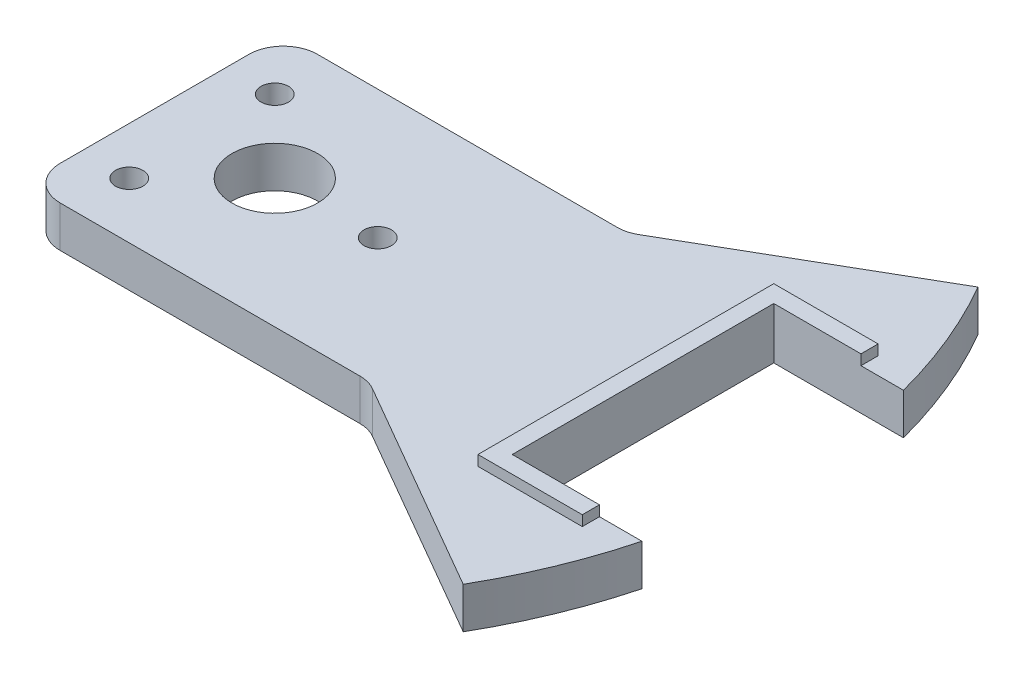
SolidWorks part; units mm, degrees
ref_plane "Front Plane" through (0, 0, 0) normal (0, 0, 1) x (1, 0, 0)
ref_plane "Top Plane" through (0, 0, 0) normal (0, 1, 0) x (1, 0, 0)
ref_plane "Right Plane" through (0, 0, 0) normal (1, 0, 0) x (0, 0, -1)
sketch "Sketch1" plane through (0, 0, 0) normal (0, 1, 0) x (1, 0, 0)
  line L0 (67.2724, 38.8397) -> (129.9038, 75)
  line L1 (0, 0) -> (150, 0) construction
  line L2 (67.2724, -38.8397) -> (129.9038, -75)
  line L4 (62.2724, 37.5) -> (-25.0481, 37.5)
  line L5 (62.2724, -37.5) -> (-25.0481, -37.5)
  line L6 (-35.0481, 27.5) -> (-35.0481, -27.5)
  line L7 (0, 0) -> (-47.1244, 0) construction
  line L8 (-21.2132, 21.2132) -> (0, 0) construction
  arc A0 (129.9038, -75) -> (129.9038, 75) centre (0, 0) ccw
  circle A1 centre (0, 0) radius 12.5
  circle A2 centre (30, 0) radius 4
  arc A5 (67.2724, 38.8397) -> (62.2724, 37.5) centre (62.2724, 47.5) cw
  arc A6 (67.2724, -38.8397) -> (62.2724, -37.5) centre (62.2724, -47.5) ccw
  arc A7 (-35.0481, -27.5) -> (-25.0481, -37.5) centre (-25.0481, -27.5) ccw
  arc A8 (-25.0481, 37.5) -> (-35.0481, 27.5) centre (-25.0481, 27.5) ccw
  circle A9 centre (-21.2132, 21.2132) radius 4
  circle A10 centre (-21.2132, -21.2132) radius 4
  point P19 (64.9519, 37.5)
  point P22 (64.9519, -37.5)
  point P25 (-35.0481, -37.5)
  point P28 (-35.0481, 37.5)
  dimension "D1" = 300
  dimension "D6" = 25
  dimension "D7" = 8
  dimension "D9" = 8
  dimension "D11" = 45
  dimension "D13" = 10
  dimension "D2" = 30
  dimension "D3" = 100
  dimension "D4" = 75
  dimension "D5" = 75
  dimension "D8" = 30
  dimension "D10" = 30
extrude "Boss-Extrude1" add sketch "Sketch1" along normal blind 12
sketch "Sketch3" plane through (0, 12, 0) normal (0, 1, 0) x (1, 0, 0)
  line L0 (0, 0) -> (150, 0) construction
  line L1 (107.3, 38.1) -> (107.3, -38.1)
  line L2 (107.3, 38.1) -> (132.7, 38.1) construction
  line L3 (107.3, 38.1) -> (107.3, -38.1) construction
  line L4 (107.3, -38.1) -> (132.7, -38.1) construction
  line L5 (132.7, 38.1) -> (132.7, -38.1) construction
  line L6 (107.3, 38.1) -> (132.7, -38.1) construction
  line L7 (107.3, -38.1) -> (132.7, 38.1) construction
  line L8 (107.3, 38.1) -> (155.3028, 38.1)
  line L9 (107.3, -38.1) -> (155.3028, -38.1)
  line L10 (155.3028, 38.1) -> (155.3028, -38.1)
  arc A0 (129.9038, -75) -> (129.9038, 75) centre (0, 0) ccw construction
  point P6 (120, 0)
  dimension "D1" = 25.4
  dimension "D2" = 76.2
  dimension "D3" = 120
extrude "Cut-Extrude5" cut sketch "Sketch3" against normal through all
sketch "Sketch4" plane through (0, 12, 0) normal (0, 1, 0) x (1, 0, 0)
  line L0 (0, 0) -> (145.9243, 0) construction
  line L1 (107.3, 38.1) -> (132.7, 38.1)
  line L3 (132.7, 38.1) -> (132.7, 43.1)
  line L4 (107.3, 43.1) -> (132.7, 43.1)
  line L5 (145.0806, 38.1) -> (107.3, 38.1) construction
  line L6 (107.3, 38.1) -> (107.3, -38.1)
  line L7 (107.3, 43.1) -> (102.3, 43.1)
  line L8 (107.3, 0) -> (102.3, 0)
  line L9 (102.3, 43.1) -> (102.3, -43.1)
  line L10 (107.3, 38.1) -> (107.3, -38.1) construction
  line L11 (132.7, -38.1) -> (132.7, -43.1)
  line L12 (107.3, -43.1) -> (132.7, -43.1)
  line L14 (107.3, -38.1) -> (132.7, -38.1)
  line L15 (107.3, -43.1) -> (102.3, -43.1)
  line M10 (107.3, 38.1) -> (145.0806, 38.1)
  line M22 (145.0806, -38.1) -> (107.3, -38.1)
  line M23 (107.3, -38.1) -> (107.3, 38.1)
  dimension "D1" = 25.4
  dimension "D2" = 5
  dimension "D3" = 5
extrude "Boss-Extrude3" add sketch "Sketch4" along normal blind 3 contours L15 L12 L11 L8 L9 M22 M23 | L7 L9 L8 L6 L3 L4 M10
